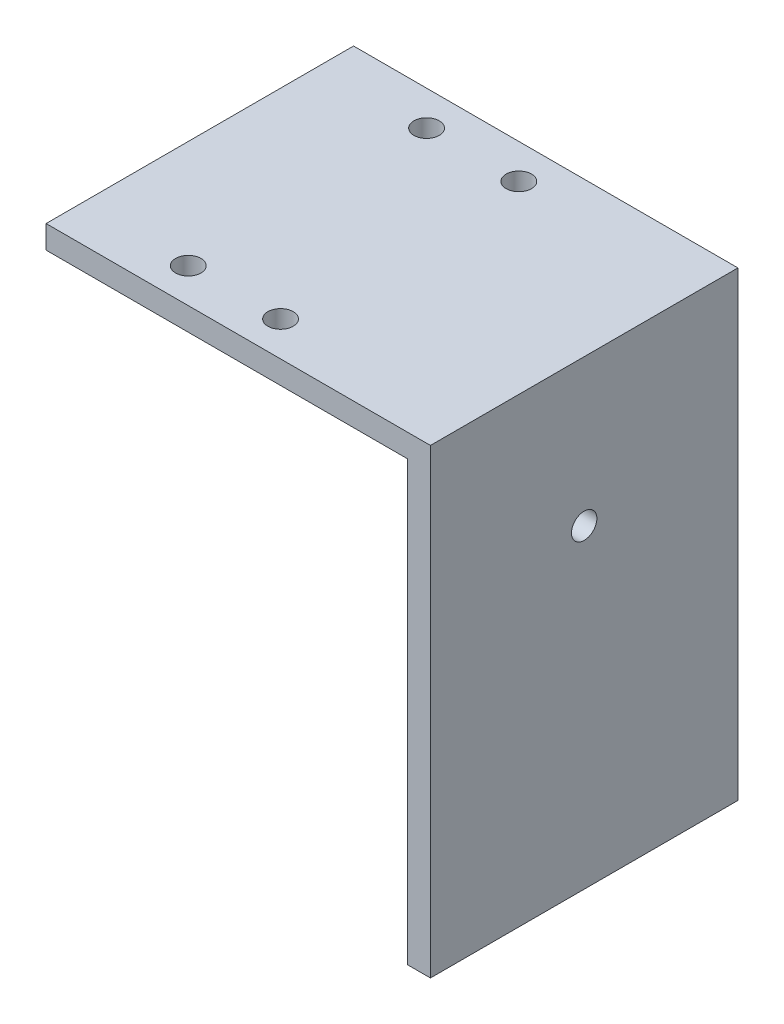
SolidWorks part; units mm, degrees
ref_plane "前视基准面" through (0, 0, 0) normal (0, 0, 1) x (1, 0, 0)
ref_plane "上视基准面" through (0, 0, 0) normal (0, 1, 0) x (1, 0, 0)
ref_plane "右视基准面" through (0, 0, 0) normal (1, 0, 0) x (0, 0, -1)
sketch "草图1" plane through (0, 0, 0) normal (0, 0, 1) x (1, 0, 0)
  line L0 (0, 0) -> (50, 0)
  line L1 (50, 0) -> (50, -60)
  line L2 (0, -3) -> (47, -3)
  line L3 (47, -3) -> (47, -60)
  line L4 (47, -60) -> (50, -60)
  line L5 (0, 0) -> (0, -3)
  dimension "D1" = 50
  dimension "D3" = 60
  dimension "D2" = 3
extrude "凸台-拉伸1" add sketch "草图1" along normal blind 40
sketch "草图2" plane through (0, 0, 0) normal (0, 1, 0) x (1, 0, 0)
  line L0 (50, -40) -> (50, 0) construction
  line L1 (14, -35.5) -> (26, -35.5) construction
  line L2 (14, -35.5) -> (14, -4.5) construction
  line L3 (14, -4.5) -> (26, -4.5) construction
  line L4 (26, -35.5) -> (26, -4.5) construction
  line L5 (14, -35.5) -> (26, -4.5) construction
  line L6 (14, -4.5) -> (26, -35.5) construction
  line L7 (20, -20) -> (50, -20) construction
  circle A0 centre (14, -4.5) radius 1.65
  circle A1 centre (14, -35.5) radius 1.65
  circle A2 centre (26, -4.5) radius 1.65
  circle A3 centre (26, -35.5) radius 1.65
  point P0 (20, -20)
  dimension "D4" = 3.3
  dimension "D1" = 24
  dimension "D2" = 12
  dimension "D3" = 31
extrude "切除-拉伸1" cut sketch "草图2" against normal blind 10
sketch "草图3" plane through (50, 0, 0) normal (1, 0, 0) x (0, 0, -1)
  line L0 (-20, 0) -> (-20, -62.884) construction
  line L1 (-40, 0) -> (0, 0) construction
  circle A0 centre (-20, -19.05) radius 1.65
  dimension "D1" = 3.3
  dimension "D2" = 19.05
extrude "切除-拉伸2" cut sketch "草图3" against normal blind 10
